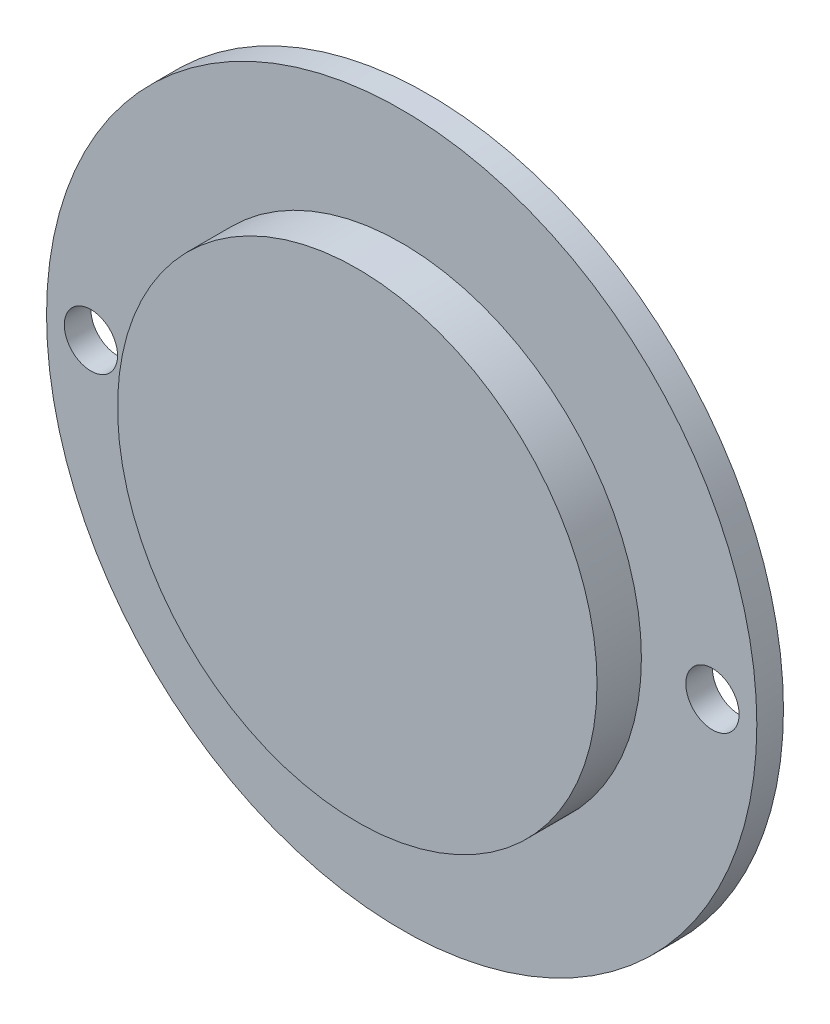
SolidWorks part; units mm, degrees
ref_plane "前视基准面" through (0, 0, 0) normal (0, 0, 1) x (1, 0, 0)
ref_plane "上视基准面" through (0, 0, 0) normal (0, 1, 0) x (1, 0, 0)
ref_plane "右视基准面" through (0, 0, 0) normal (1, 0, 0) x (0, 0, -1)
sketch "草图1" plane through (0, 0, 0) normal (0, 0, 1) x (1, 0, 0)
  circle A0 centre (0, 0) radius 40
  dimension "D1" = 80
extrude "凸台-拉伸1" add sketch "草图1" along normal blind 3
sketch "草图2" plane through (0, 0, 3) normal (0, 0, 1) x (1, 0, 0)
  circle A0 centre (0, 0) radius 27
  dimension "D1" = 54
extrude "凸台-拉伸2" add sketch "草图2" along normal blind 5
sketch "草图3" plane through (0, 0, 0) normal (0, 0, -1) x (-1, 0, 0)
  line L0 (0, 0) -> (0, -15.2684) construction
  circle A0 centre (35, 0) radius 3
  circle A1 centre (-35, 0) radius 3
  dimension "D1" = 6
  dimension "D2" = 70
extrude "切除-拉伸1" cut sketch "草图3" against normal blind 5
